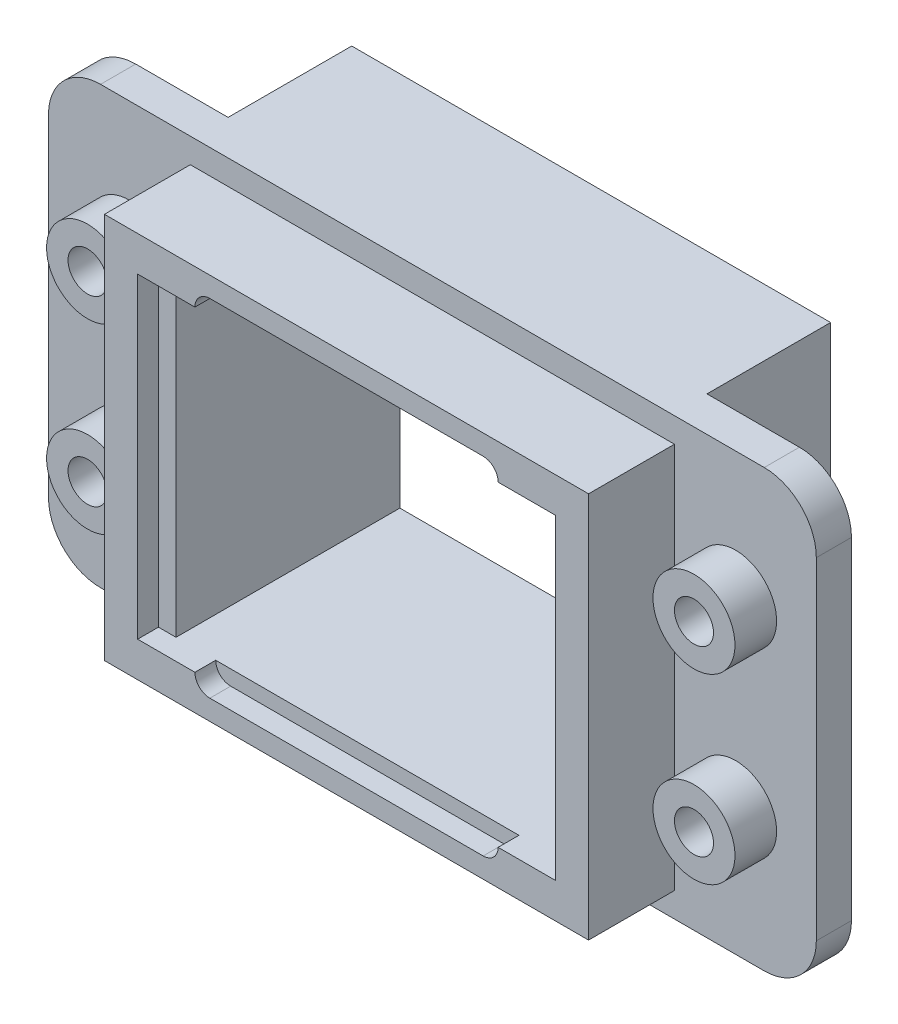
SolidWorks part; units mm, degrees
ref_plane "Спереди" through (0, 0, 0) normal (0, 0, 1) x (1, 0, 0)
ref_plane "Сверху" through (0, 0, 0) normal (0, 1, 0) x (1, 0, 0)
ref_plane "Справа" through (0, 0, 0) normal (1, 0, 0) x (0, 0, -1)
sketch "Эскиз1" plane through (0, 0, 0) normal (0, 0, 1) x (1, 0, 0)
  line L1 (-12.75, -8.375) -> (12.75, -8.375)
  line L2 (-14.75, -6.375) -> (-14.75, 6.375)
  line L3 (-12.75, 8.375) -> (12.75, 8.375)
  line L4 (14.75, -6.375) -> (14.75, 6.375)
  line L5 (-14.75, -8.375) -> (14.75, 8.375) construction
  line L6 (-14.75, 8.375) -> (14.75, -8.375) construction
  arc A0 (-12.75, -8.375) -> (-14.75, -6.375) centre (-12.75, -6.375) cw
  arc A1 (12.75, -8.375) -> (14.75, -6.375) centre (12.75, -6.375) ccw
  arc A2 (12.75, 8.375) -> (14.75, 6.375) centre (12.75, 6.375) cw
  arc A3 (-14.75, 6.375) -> (-12.75, 8.375) centre (-12.75, 6.375) cw
  point P0 (0, 0)
  dimension "D3" = 2
  dimension "D1" = 29.5
  dimension "D2" = 16.75
extrude "Бобышка-Вытянуть1" add sketch "Эскиз1" along normal blind 1.35
sketch "Эскиз8" plane through (0, 0, 0) normal (0, 0, -1) x (-1, 0, 0)
  line L0 (12.75, -8.375) -> (-12.75, -8.375) construction
  line L1 (9.2, 8.375) -> (-9.2, 8.375)
  line L2 (9.2, 8.375) -> (9.2, -8.375)
  line L3 (9.2, -8.375) -> (-9.2, -8.375)
  line L4 (-9.2, 8.375) -> (-9.2, -8.375)
  line L5 (9.2, 8.375) -> (-9.2, -8.375) construction
  line L6 (9.2, -8.375) -> (-9.2, 8.375) construction
  point P0 (0, 0)
  dimension "D1" = 18.4
extrude "Бобышка-Вытянуть4" add sketch "Эскиз8" along normal blind 4.75
sketch "Эскиз2" plane through (0, 0, 1.35) normal (0, 0, 1) x (1, 0, 0)
  line L0 (0, 0) -> (0, 9.8387) construction
  line L1 (0, 0) -> (9.7136, 0) construction
  circle A0 centre (-11.65, 3.5) radius 1.575
  circle A1 centre (11.65, 3.5) radius 1.575
  circle A2 centre (11.65, -3.5) radius 1.575
  circle A3 centre (-11.65, -3.5) radius 1.575
  point P12 (0, 0)
  point P13 (0, 0)
  point P14 (0, 0)
  point P15 (0, 0)
  dimension "D1" = 3.15
  dimension "D2" = 7
  dimension "D3" = 23.3
extrude "Бобышка-Вытянуть2" add sketch "Эскиз2" along normal blind 1.6
sketch "Эскиз4" plane through (0, 0, 1.35) normal (0, 0, 1) x (1, 0, 0)
  line L1 (-9.3, -7.425) -> (9.3, -7.425)
  line L2 (-9.3, -7.425) -> (-9.3, 7.425)
  line L3 (-9.3, 7.425) -> (9.3, 7.425)
  line L4 (9.3, -7.425) -> (9.3, 7.425)
  line L5 (-9.3, -7.425) -> (9.3, 7.425) construction
  line L6 (-9.3, 7.425) -> (9.3, -7.425) construction
  point P0 (0, 0)
  dimension "D1" = 18.6
  dimension "D2" = 14.85
extrude "Бобышка-Вытянуть3" add sketch "Эскиз4" along normal blind 3.3
sketch "Эскиз3" plane through (0, 0, 4.65) normal (0, 0, 1) x (1, 0, 0)
  line L1 (-7.35, -6.075) -> (7.35, -6.075)
  line L2 (-7.35, -6.075) -> (-7.35, 6.075)
  line L3 (-7.35, 6.075) -> (7.35, 6.075)
  line L4 (7.35, -6.075) -> (7.35, 6.075)
  line L5 (-7.35, -6.075) -> (7.35, 6.075) construction
  line L6 (-7.35, 6.075) -> (7.35, -6.075) construction
  point P0 (0, 0)
  dimension "D1" = 14.7
  dimension "D2" = 12.15
extrude "Вырез-Вытянуть1" cut sketch "Эскиз3" against normal through all
sketch "Эскиз5" plane through (0, 0, 4.65) normal (0, 0, 1) x (1, 0, 0)
  line L0 (-5.25, 6.075) -> (5.25, 6.075) construction
  line L1 (7.35, 6.075) -> (-7.35, 6.075) construction
  line L2 (-5.25, 6.65) -> (5.25, 6.65)
  line L3 (-5.25, 5.5) -> (5.25, 5.5)
  line L4 (0, 0) -> (17.0697, 0) construction
  line L5 (-5.25, -6.075) -> (5.25, -6.075) construction
  line L6 (-5.25, -6.65) -> (5.25, -6.65)
  line L7 (-5.25, -5.5) -> (5.25, -5.5)
  line L8 (-7.35, 6.075) -> (-7.35, -6.075) construction
  line L9 (-8.025, 6.075) -> (-7.35, 6.075)
  line L10 (-8.025, 6.075) -> (-8.025, -6.075)
  line L11 (-8.025, -6.075) -> (-7.35, -6.075)
  line L12 (-7.35, 6.075) -> (-7.35, -6.075)
  line L13 (7.35, 6.075) -> (8.025, 6.075)
  line L14 (7.35, 6.075) -> (7.35, -6.075)
  line L15 (7.35, -6.075) -> (8.025, -6.075)
  line L16 (8.025, 6.075) -> (8.025, -6.075)
  line L17 (7.35, -6.075) -> (7.35, 6.075) construction
  arc A0 (-5.25, 6.65) -> (-5.25, 5.5) centre (-5.25, 6.075) ccw
  arc A1 (5.25, 5.5) -> (5.25, 6.65) centre (5.25, 6.075) ccw
  arc A2 (-5.25, -6.65) -> (-5.25, -5.5) centre (-5.25, -6.075) cw
  arc A3 (5.25, -5.5) -> (5.25, -6.65) centre (5.25, -6.075) cw
  point P4 (0, 6.075)
  point P14 (0, -6.075)
  point P29 (0, 0)
  point P30 (-7.35, 6.075)
  point P33 (-7.35, 6.075)
  point P34 (7.35, -6.075)
  point P37 (7.35, -6.075)
  point P38 (7.35, -6.075)
  dimension "D1" = 13.3
  dimension "D2" = 10.5
  dimension "D3" = 16.05
extrude "Вырез-Вытянуть2" cut sketch "Эскиз5" against normal blind 0.8
sketch "Эскиз6" plane through (0, 0, 2.95) normal (0, 0, 1) x (1, 0, 0)
  circle A0 centre (-11.65, 3.5) radius 0.75
  circle A1 centre (-11.65, -3.5) radius 0.75
  circle A2 centre (11.65, 3.5) radius 0.75
  circle A3 centre (11.65, -3.5) radius 0.75
  dimension "D1" = 1.5
extrude "Вырез-Вытянуть3" cut sketch "Эскиз6" against normal through all
